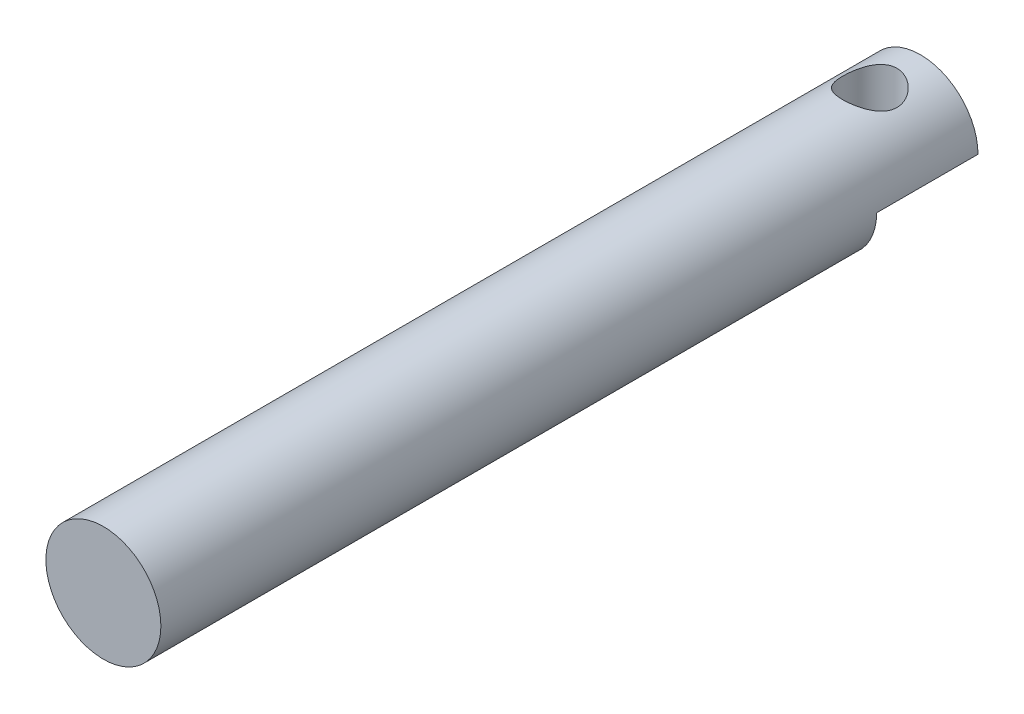
SolidWorks part; units mm, degrees
ref_plane "Front Plane" through (0, 0, 0) normal (0, 0, 1) x (1, 0, 0)
ref_plane "Top Plane" through (0, 0, 0) normal (0, 1, 0) x (1, 0, 0)
ref_plane "Right Plane" through (0, 0, 0) normal (1, 0, 0) x (0, 0, -1)
sketch "Sketch1" plane through (0, 0, 0) normal (0, 0, 1) x (1, 0, 0)
  circle A0 centre (0, 0) radius 3.175
  dimension "D1" = 6.35
extrude "Boss-Extrude1" add sketch "Sketch1" along normal blind 45.12
sketch "Sketch2" plane through (0, 0, 0) normal (0, 1, 0) x (1, 0, 0)
  line L0 (3.175, -45.12) -> (3.175, 0) construction
  line L1 (-3.175, 0) -> (3.175, 0)
  line L2 (-3.175, 0) -> (-3.175, -5.5973)
  line L3 (-3.175, -5.5973) -> (3.175, -5.5973)
  line L4 (3.175, 0) -> (3.175, -5.5973)
extrude "Cut-Extrude1" cut sketch "Sketch2" against normal blind 7
sketch "Sketch3" plane through (0, 0, 0) normal (0, -1, 0) x (1, 0, 0)
  line L1 (-3.175, 0) -> (-3.175, 5.5973) construction
  circle A0 centre (0, 2.7986) radius 1.5
  point P2 (0, 0)
  point P3 (0, 0)
  point P9 (-3.175, 2.7986)
  dimension "D1" = 3
extrude "Cut-Extrude2" cut sketch "Sketch3" against normal blind 7
